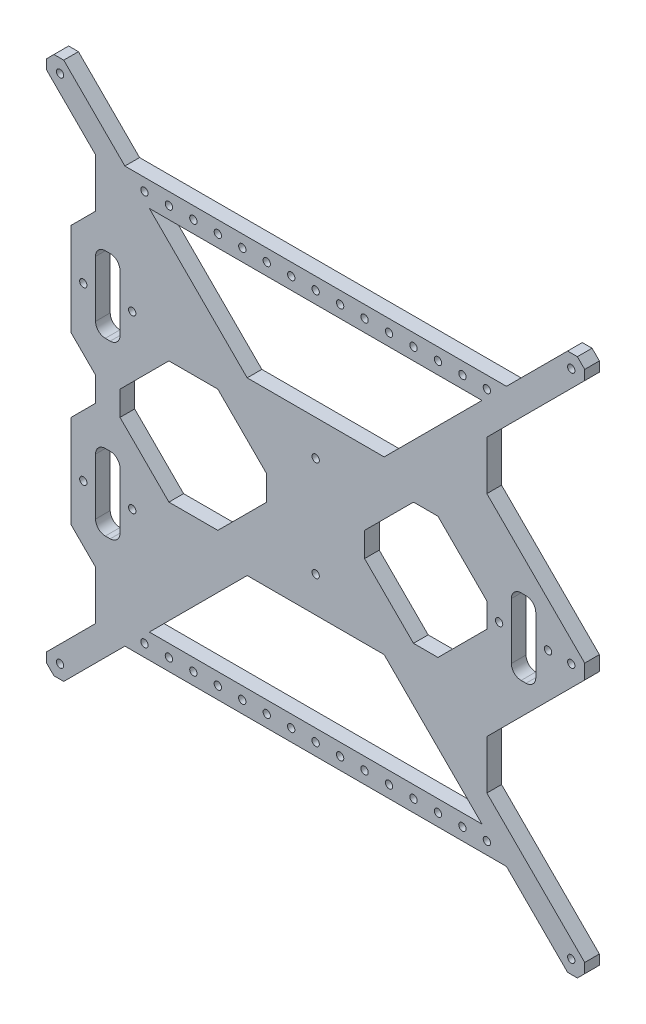
SolidWorks part; units mm, degrees
ref_plane "Alzado" through (0, 0, 0) normal (0, 0, 1) x (1, 0, 0)
ref_plane "Planta" through (0, 0, 0) normal (0, 1, 0) x (1, 0, 0)
ref_plane "Vista lateral" through (0, 0, 0) normal (1, 0, 0) x (0, 0, -1)
sketch "Model" plane through (0, 0, 0) normal (0, 0, 1) x (1, 0, 0)
  line L34 (-105, 110) -> (-107, 110)
  line L35 (-107, 110) -> (-110, 107)
  line L36 (-110, 107) -> (-110, 105)
  line L37 (-110, 105) -> (-110, 103)
  line L38 (-110, 103) -> (-90, 83)
  line L39 (-90, 83) -> (-90, 63)
  line L40 (-90, 63) -> (-100, 53)
  line L41 (-100, -53) -> (-90, -63)
  line L42 (-110, -103) -> (-90, -83)
  line L43 (-90, -83) -> (-90, -63)
  line L44 (-110, -103) -> (-110, -107)
  line L45 (-110, -107) -> (-107, -110)
  line L46 (-107, -110) -> (-105, -110)
  line L47 (105, -110) -> (107, -110)
  line L48 (107, -110) -> (110, -107)
  line L49 (110, 106) -> (110, 107)
  line L50 (110, 107) -> (107, 110)
  line L51 (110, 103) -> (70, 63)
  line L52 (110, 3) -> (90, 23)
  line L53 (90, 23) -> (70, 43)
  line L54 (70, 43) -> (70, 63)
  line L55 (110, -3) -> (90, -23)
  line L56 (90, -23) -> (70, -43)
  line L57 (110, -103) -> (90, -83)
  line L58 (90, -83) -> (70, -63)
  line L59 (70, -63) -> (70, -43)
  line L60 (103, 110) -> (80, 87)
  line L61 (40, 47) -> (38, 45)
  line L62 (38, 45) -> (28, 35)
  line L63 (28, 35) -> (-28, 35)
  line L64 (103, -110) -> (78, -85)
  line L65 (28, -35) -> (-28, -35)
  line L66 (-78, 85) -> (78, 85)
  line L67 (-78, -85) -> (78, -85)
  line L68 (-100, 15) -> (-90, 5)
  line L69 (-90, 5) -> (-90, -5)
  line L70 (-90, -5) -> (-100, -15)
  line L71 (-80, 5) -> (-60, 25)
  line L72 (-60, 25) -> (-40, 25)
  line L73 (-40, 25) -> (-20, 5)
  line L74 (-20, 5) -> (-20, -5)
  line L75 (-20, -5) -> (-40, -25)
  line L76 (-40, -25) -> (-60, -25)
  line L77 (-60, -25) -> (-80, -5)
  line L78 (-80, -5) -> (-80, 5)
  line L79 (50, 25) -> (70, 5)
  line L80 (70, 5) -> (70, -5)
  line L81 (70, -5) -> (50, -25)
  line L82 (50, -25) -> (40, -25)
  line L83 (40, -25) -> (20, -5)
  line L84 (20, -5) -> (20, 5)
  line L85 (20, 5) -> (40, 25)
  line L86 (40, 25) -> (50, 25)
  line L87 (-105, 110) -> (-103, 110)
  line L88 (107, 110) -> (103, 110)
  line L89 (110, 106) -> (110, 103)
  line L90 (110, -103) -> (110, -107)
  line L91 (103, -110) -> (105, -110)
  line L92 (-103, -110) -> (-105, -110)
  line L93 (-68, 75) -> (68, 75)
  line L94 (80, 87) -> (78, 85)
  line L95 (68, 75) -> (40, 47)
  line L96 (-103, 110) -> (-78, 85)
  line L97 (-68, 75) -> (-28, 35)
  line L98 (68, -75) -> (-68, -75)
  line L99 (-103, -110) -> (-78, -85)
  line L100 (-28, -35) -> (-68, -75)
  line L101 (28, -35) -> (68, -75)
  line L171 (-100, 53) -> (-100, 15)
  line L172 (-100, -15) -> (-100, -53)
  line L173 (110, 3) -> (110, -3)
  line L180 (-90, -46) -> (-90, -23)
  line L181 (-86, -19) -> (-84, -19)
  line L182 (-80, -23) -> (-80, -46)
  line L183 (-84, -50) -> (-86, -50)
  line L184 (-90, 24.007) -> (-90, 47.007)
  line L185 (-86, 51.007) -> (-84, 51.007)
  line L186 (-80, 47.007) -> (-80, 24.007)
  line L187 (-84, 20.007) -> (-86, 20.007)
  line L188 (80, -12.1371) -> (80, 10.8629)
  line L189 (84, 14.8629) -> (86, 14.8629)
  line L190 (90, 10.8629) -> (90, -12.1371)
  line L191 (86, -16.1371) -> (84, -16.1371)
  circle A0 centre (104.5, 0) radius 1.5
  circle A6 centre (-95, 35) radius 1.5
  circle A7 centre (-75, 35) radius 1.5
  circle A8 centre (-95, -35) radius 1.5
  circle A9 centre (-75, -35) radius 1.5
  circle A10 centre (95, 0) radius 1.5
  circle A11 centre (75, 0) radius 1.5
  circle A12 centre (-104.5, 104.5) radius 1.5
  circle A13 centre (104.5, -104.5) radius 1.5
  circle A14 centre (104.5, 104.5) radius 1.5
  circle A15 centre (-104.5, -104.5) radius 1.5
  arc A20 (-86, -19) -> (-90, -23) centre (-86, -23) ccw
  arc A21 (-80, -23) -> (-84, -19) centre (-84, -23) ccw
  arc A22 (-90, -46) -> (-86, -50) centre (-86, -46) ccw
  arc A23 (-84, -50) -> (-80, -46) centre (-84, -46) ccw
  circle A34 centre (0, -20.5) radius 1.5
  circle A35 centre (0, 20.5) radius 1.5
  arc A36 (-84, 20.007) -> (-80, 24.007) centre (-84, 24.007) ccw
  arc A37 (-86, 51.007) -> (-90, 47.007) centre (-86, 47.007) ccw
  arc A38 (-80, 47.007) -> (-84, 51.007) centre (-84, 47.007) ccw
  arc A39 (-90, 24.007) -> (-86, 20.007) centre (-86, 24.007) ccw
  arc A40 (86, -16.1371) -> (90, -12.1371) centre (86, -12.1371) ccw
  arc A41 (84, 14.8629) -> (80, 10.8629) centre (84, 10.8629) ccw
  arc A42 (90, 10.8629) -> (86, 14.8629) centre (86, 10.8629) ccw
  arc A43 (80, -12.1371) -> (84, -16.1371) centre (84, -12.1371) ccw
  dimension "D1" = 20.5
  dimension "D2" = 20.5
  dimension "D3" = 35
  dimension "D4" = 35
extrude "Saliente-Extruir1" add sketch "Model" along normal blind 6
sketch "Croquis2" plane through (0, 0, 0) normal (0, 0, -1) x (-1, 0, 0)
  line L0 (0, 85) -> (0, 75) construction
  line L1 (-78, 85) -> (78, 85) construction
  line L2 (-68, 75) -> (68, 75) construction
  line L3 (0, 80) -> (-87, 80) construction
  line L4 (-70, 63) -> (-110, 103) construction
  line L5 (-70, -80) -> (-60, -80) construction
  line L7 (-70, 63) -> (-70, 80) construction
  line L8 (-70, -63) -> (-70, -85) construction
  line L9 (78, -85) -> (-78, -85) construction
  line L10 (0, -75) -> (0, -85) construction
  line L11 (68, -75) -> (-68, -75) construction
  line L12 (0, -80) -> (-87, -80) construction
  line L13 (-110, -103) -> (-70, -63) construction
  circle A0 centre (-70, 80) radius 1.5
  circle A1 centre (-70, -80) radius 1.5
  circle A2 centre (-61.5067, -90.7338) radius 0.2417
  circle A3 centre (-60, -80) radius 1.5
  circle A4 centre (-60, 80) radius 1.5
  circle A5 centre (-50, -80) radius 1.5
  circle A6 centre (-50, 80) radius 1.5
  circle A7 centre (-40, -80) radius 1.5
  circle A8 centre (-40, 80) radius 1.5
  circle A9 centre (-30, -80) radius 1.5
  circle A10 centre (-30, 80) radius 1.5
  circle A11 centre (-20, -80) radius 1.5
  circle A12 centre (-20, 80) radius 1.5
  circle A13 centre (-10, -80) radius 1.5
  circle A14 centre (-10, 80) radius 1.5
  circle A15 centre (0, -80) radius 1.5
  circle A16 centre (0, 80) radius 1.5
  circle A17 centre (10, -80) radius 1.5
  circle A18 centre (10, 80) radius 1.5
  circle A19 centre (20, -80) radius 1.5
  circle A20 centre (20, 80) radius 1.5
  circle A21 centre (30, -80) radius 1.5
  circle A22 centre (30, 80) radius 1.5
  circle A23 centre (40, -80) radius 1.5
  circle A24 centre (40, 80) radius 1.5
  circle A25 centre (50, -80) radius 1.5
  circle A26 centre (50, 80) radius 1.5
  circle A27 centre (60, -80) radius 1.5
  circle A28 centre (60, 80) radius 1.5
  circle A29 centre (70, -80) radius 1.5
  circle A30 centre (70, 80) radius 1.5
  dimension "D1" = 3
  dimension "D2" = 15
  dimension "D3" = 10
extrude "Cortar-Extruir1" cut sketch "Croquis2" against normal through all
